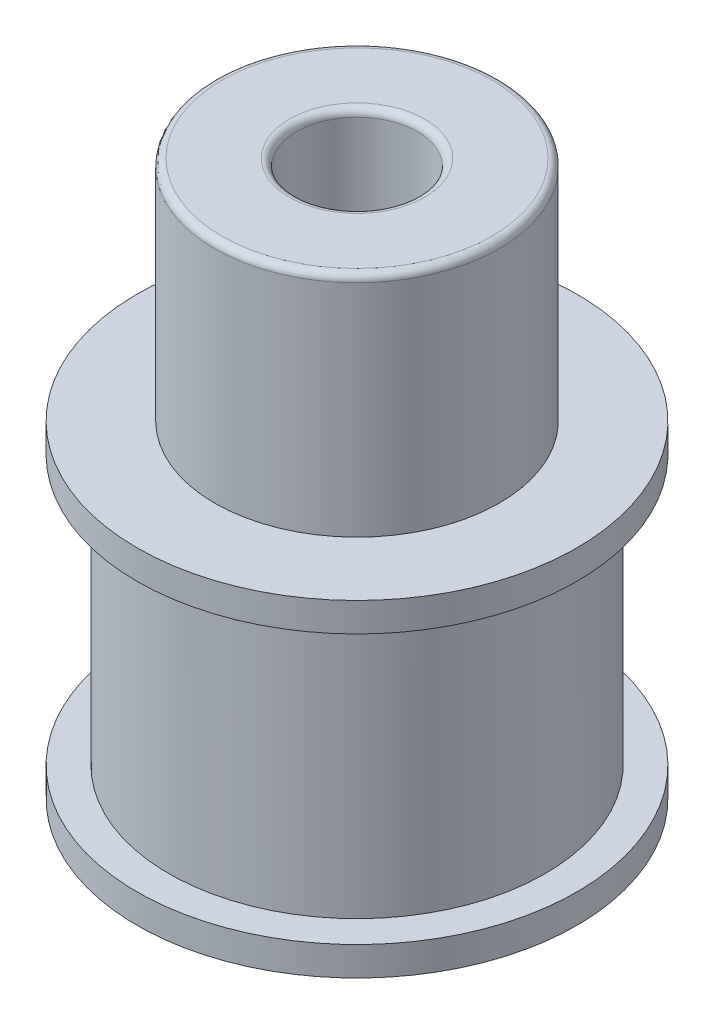
SolidWorks part; units mm, degrees
ref_plane "Front" through (0, 0, 0) normal (0, 0, 1) x (1, 0, 0)
ref_plane "Top" through (0, 0, 0) normal (0, 1, 0) x (1, 0, 0)
ref_plane "Right" through (0, 0, 0) normal (1, 0, 0) x (0, 0, -1)
sketch "Sketch1" plane through (0, 0, 0) normal (0, 1, 0) x (1, 0, 0)
  circle A0 centre (0, 0) radius 9.09
  dimension "D1" = 18.18
extrude "Boss-Extrude1" add sketch "Sketch1" along normal blind 13.52
sketch "Sketch2" plane through (0, 13.52, 0) normal (0, 1, 0) x (1, 0, 0)
  circle A0 centre (0, 0) radius 5.885
  dimension "D1" = 11.77
extrude "Boss-Extrude2" add sketch "Sketch2" along normal blind 9.41
sketch "Sketch3" plane through (0, 0, 0) normal (0, -1, 0) x (1, 0, 0)
  circle A0 centre (0, 0) radius 7.78
  dimension "D1" = 15.56
extrude "Cut-Extrude1" cut sketch "Sketch3" along direction (0, 1, 0) on the side against the normal offset from surface (12.32 mm away) 1.2 flip side to cut
sketch "Sketch4" plane through (0, 0, 0) normal (0, -1, 0) x (1, 0, 0)
  circle A0 centre (0, 0) radius 9.09
  dimension "D1" = 18.18
extrude "Boss-Extrude3" add sketch "Sketch4" against normal blind 1.2
sketch "Sketch5" plane through (0, 0, 0) normal (0, -1, 0) x (1, 0, 0)
  circle A0 centre (0, 0) radius 2.5
  dimension "D1" = 5
extrude "Cut-Extrude2" cut sketch "Sketch5" against normal through all
fillet "Fillet3" radius 0.3 3 edges at (0, 22.93, 5.885) (0, 22.93, -2.5) (0, 0, -2.5)
